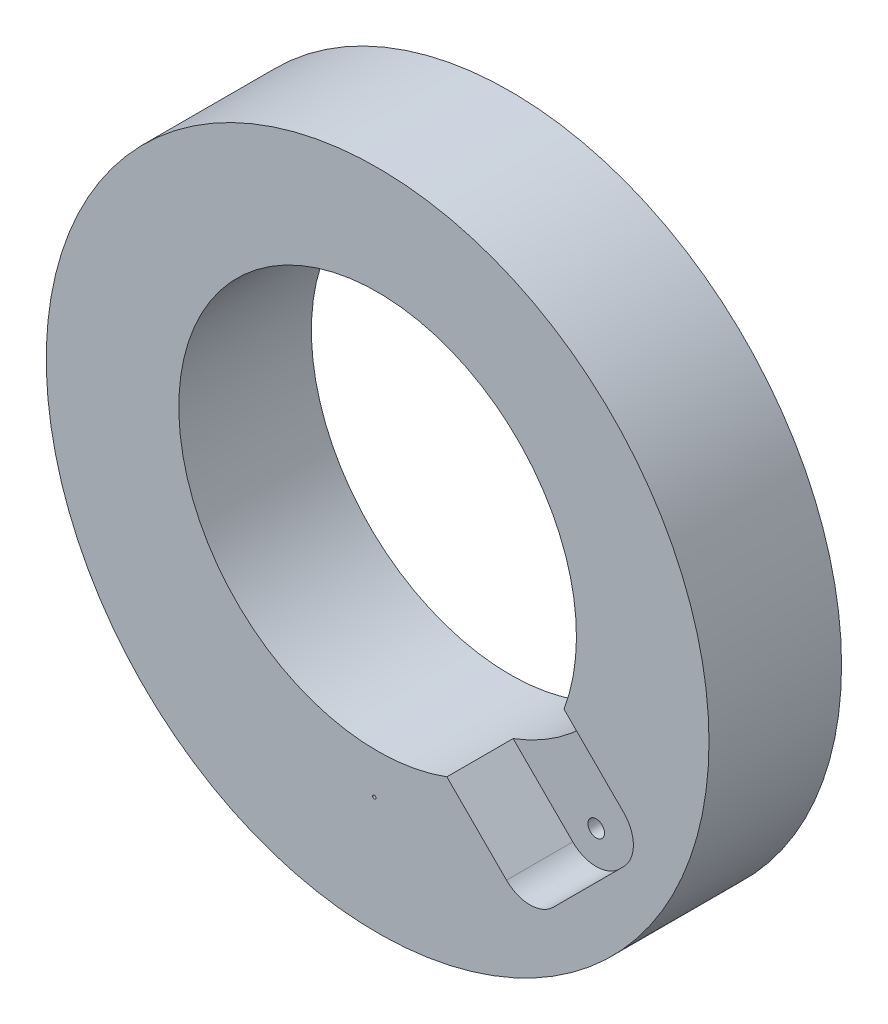
SolidWorks part; units mm, degrees
material "St37-2"
ref_plane "Vorder" through (0, 0, 0) normal (0, 0, 1) x (1, 0, 0)
ref_plane "Drauf" through (0, 0, 0) normal (0, 1, 0) x (1, 0, 0)
ref_plane "Seite" through (0, 0, 0) normal (1, 0, 0) x (0, 0, -1)
sketch "Skizze1" plane through (0, 0, 0) normal (0, 0, 1) x (1, 0, 0)
  circle A0 centre (0, 0) radius 100
  circle A1 centre (0, 7.5) radius 60
  dimension "D1" = 200
  dimension "D2" = 7.5
  dimension "D3" = 120
extrude "Basis-Linear austragen" add sketch "Skizze1" along normal blind 40
sketch "Skizze2" plane through (0, 0, 40) normal (0, 0, 1) x (1, 0, 0)
  line L0 (0, 7.5) -> (60.3072, -52.8072) construction
  line L1 (0, 7.5) -> (0, 37.575) construction
  line L2 (17.2722, -45.1276) -> (52.6276, -9.7722)
  line L3 (17.2722, -45.1276) -> (38.8909, -66.7462)
  line L4 (52.6276, -9.7722) -> (74.2462, -31.3909)
  line L5 (53.033, -66.7462) -> (74.2462, -45.533)
  arc A0 (74.2462, -31.3909) -> (74.2462, -45.533) centre (67.1751, -38.4619) cw
  arc A1 (38.8909, -66.7462) -> (53.033, -66.7462) centre (45.9619, -59.6751) ccw
  point P11 (81.3173, -38.4619)
  point P14 (45.9619, -73.8173)
  dimension "D4" = 10
  dimension "D1" = 135
  dimension "D2" = 50
  dimension "D3" = 90
extrude "Schnitt-Linear austragen1" cut sketch "Skizze2" against normal blind 20
sketch "Skizze4" plane through (0, 0, 40) normal (0, 0, 1) x (1, 0, 0)
  line L0 (0, 0) -> (0, -65) construction
  line L1 (0, 0) -> (-1, -64.9923) construction
  circle A0 centre (0, 0) radius 65 construction
  circle A1 centre (-1, -64.9923) radius 0.5
  dimension "TD" = 130
  dimension "BD" = 1
  dimension "AX" = 1
extrude "Schnitt-Linear austragen3" cut sketch "Skizze4" against normal through all
hole_wizard "M6x1.0 Gewindekernloch1" positions "Skizze7" profile "Skizze6" tap size "M6x1.0" standard "DIN" end condition through all
sketch "Skizze7" plane through (0, 0, 20) normal (0, 0, 1) x (1, 0, 0)
  point P0 (45.9619, -59.6751)
  point P1 (67.1751, -38.4619)
sketch "Skizze6" plane through (45.9619, -59.6751, 20) normal (1, 0, 0) x (0, -1, 0)
  line L0 (0, 0) -> (0, 20)
  line L1 (0, 20) -> (2.5, 20)
  line L2 (2.5, 20) -> (2.5, 0)
  line L5 (2.5, 0) -> (0, 0)
  line L11 (0, -6.35) -> (0, 107.95) construction
  dimension "Bohrerdurchmesser" = 5
  dimension "Bohrungstiefe" = 20
cosmetic thread "Gewindedarstellung1" parameters "D2"=6
cosmetic thread "Gewindedarstellung2" parameters "D2"=6
